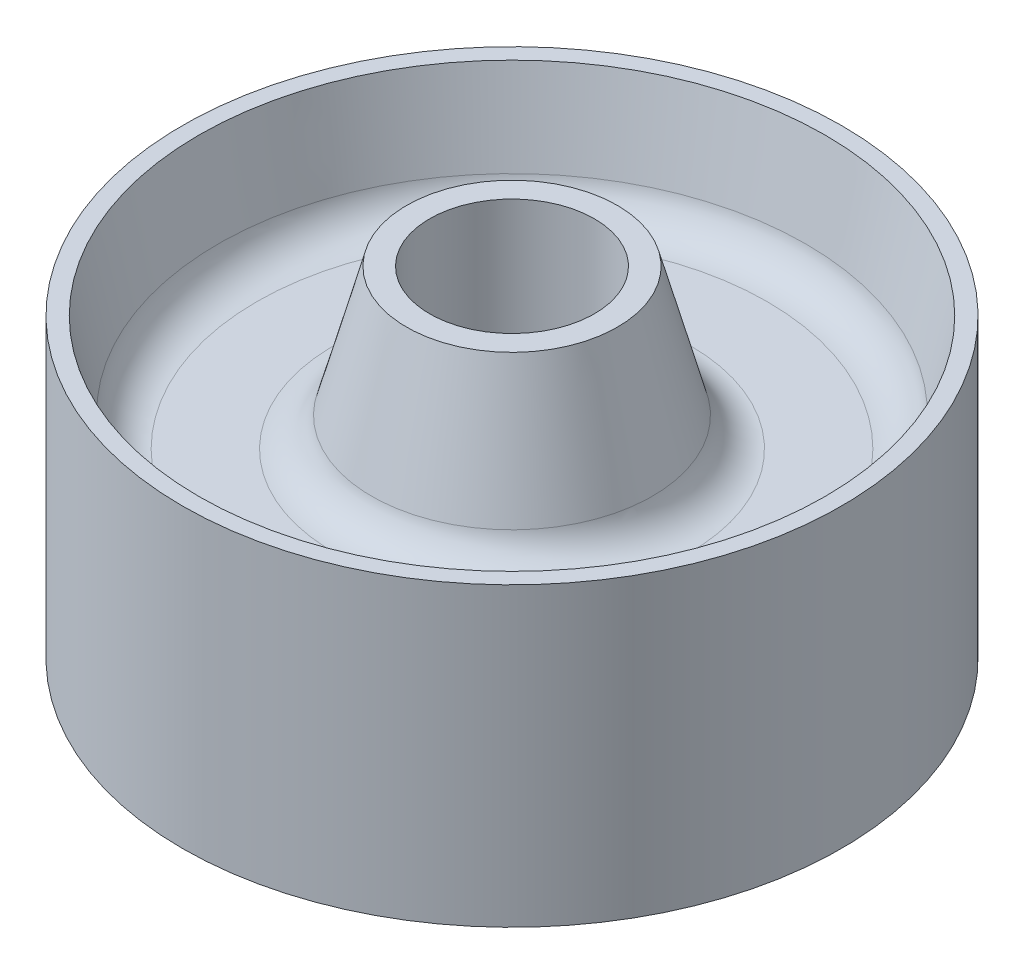
SolidWorks part; units mm, degrees
ref_plane "Front Plane" through (0, 0, 0) normal (0, 0, 1) x (1, 0, 0)
ref_plane "Top Plane" through (0, 0, 0) normal (0, 1, 0) x (1, 0, 0)
ref_plane "Right Plane" through (0, 0, 0) normal (1, 0, 0) x (0, 0, -1)
sketch "Sketch1" plane through (0, 0, 0) normal (0, 0, 1) x (1, 0, 0)
  line L0 (12.5, 0) -> (16, 0)
  line L1 (16, 0) -> (21.2998, 19.5685)
  line L2 (27.0912, 24) -> (38.7167, 24)
  line L3 (44.5658, 19.3369) -> (47.5, 6.5)
  line L4 (47.5, 6.5) -> (50, 6.5)
  line L5 (50, 6.5) -> (50, 51.5)
  line L6 (50, 51.5) -> (47.5, 51.5)
  line L7 (47.5, 51.5) -> (44.5658, 38.6631)
  line L8 (38.7167, 34) -> (27.0912, 34)
  line L9 (21.2998, 38.4315) -> (16, 58)
  line L10 (16, 58) -> (12.5, 58)
  line L11 (12.5, 58) -> (12.5, 0)
  line L12 (0, 0) -> (0, 32.5492) construction
  arc A0 (21.2998, 19.5685) -> (27.0912, 24) centre (27.0912, 18) cw
  arc A1 (38.7167, 24) -> (44.5658, 19.3369) centre (38.7167, 18) cw
  arc A2 (44.5658, 38.6631) -> (38.7167, 34) centre (38.7167, 40) cw
  arc A3 (27.0912, 34) -> (21.2998, 38.4315) centre (27.0912, 40) cw
  point P15 (0, 0)
  point P16 (0, 0)
  point P17 (0, 0)
  point P18 (0, 0)
  point P19 (0, 0)
  point P20 (27.3906, 26.3175)
  point P21 (0, 0)
  point P22 (45.6068, 38.4113)
  point P23 (44.473, 16.3175)
  point P24 (12.5, 29)
  point P25 (0, 0)
  point P26 (18.6524, 34)
  point P29 (22.5, 24)
  point P32 (43.5, 24)
  point P35 (43.5, 34)
  point P38 (22.5, 34)
  point P39 (0, 0)
  point P40 (0, 0)
  point P41 (0, 0)
  point P42 (0, 0)
  point P43 (0, 0)
  point P44 (0, 0)
  point P45 (0, 0)
  dimension "D9" = 6
  dimension "D1" = 32
  dimension "D2" = 10
  dimension "D3" = 100
  dimension "D4" = 45
  dimension "D5" = 58
  dimension "D6" = 5
  dimension "D7" = 22.5
  dimension "D8" = 25
  dimension "D10" = 95
  dimension "D11" = 45
  dimension "D12" = 87
revolve "Revolve1" add sketch "Sketch1" angle 360 about L12
